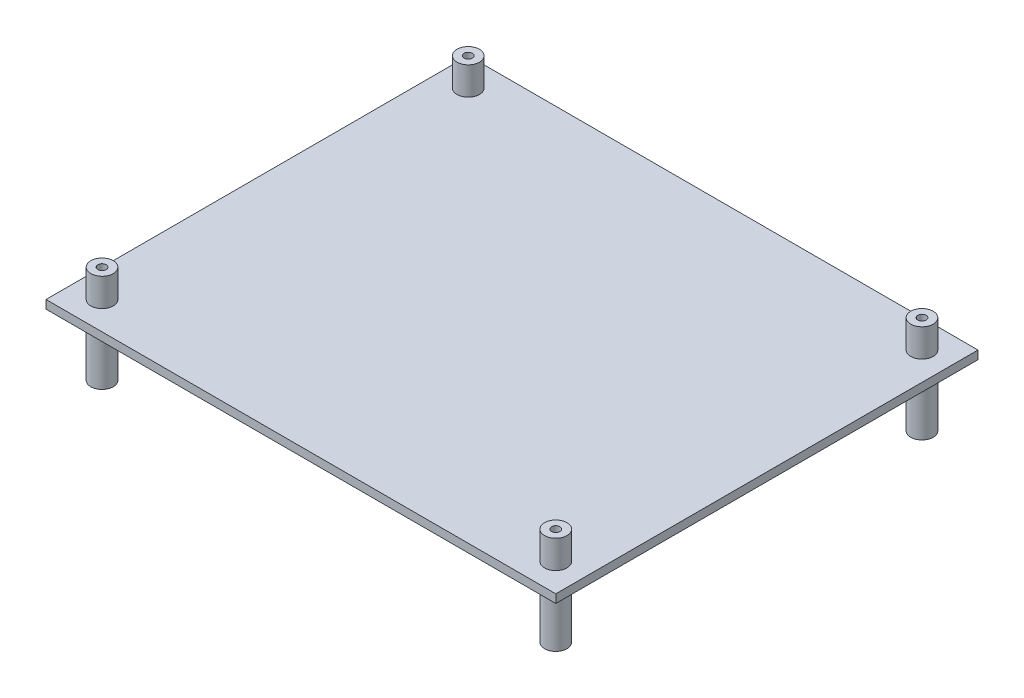
SolidWorks part; units mm, degrees
ref_plane "Front Plane" through (0, 0, 0) normal (0, 0, 1) x (1, 0, 0)
ref_plane "Top Plane" through (0, 0, 0) normal (0, 1, 0) x (1, 0, 0)
ref_plane "Right Plane" through (0, 0, 0) normal (1, 0, 0) x (0, 0, -1)
sketch "Sketch1" plane through (0, 0, 0) normal (0, 1, 0) x (1, 0, 0)
  line L0 (-10, -10) -> (-10, 140.7502)
  line L1 (0, 0) -> (162, 0) construction
  line L2 (0, 0) -> (0, 130.7502) construction
  line L3 (0, 130.7502) -> (162, 130.7502) construction
  line L4 (162, 0) -> (162, 130.7502) construction
  line L5 (-10, 140.7502) -> (172, 140.7502)
  line L6 (172, -10) -> (172, 140.7502)
  line L7 (-10, -10) -> (172, -10)
  circle A0 centre (0, 130.7502) radius 1.5
  circle A1 centre (162, 130.7502) radius 1.5
  circle A2 centre (162, 0) radius 1.5
  circle A3 centre (0, 0) radius 1.5
  dimension "D3" = 3
  dimension "D1" = 130.7502
  dimension "D2" = 162
  dimension "D4" = 10
extrude "Boss-Extrude1" add sketch "Sketch1" along normal blind 3
sketch "Sketch2" plane through (0, 3, 0) normal (0, 1, 0) x (1, 0, 0)
  circle A0 centre (0, 130.7502) radius 4
  circle A1 centre (162, 130.7502) radius 4
  circle A2 centre (162, 0) radius 4
  circle A3 centre (0, 0) radius 4
  circle A4 centre (0, 130.7502) radius 1.5 construction
  circle A5 centre (162, 130.7502) radius 1.5 construction
  circle A6 centre (162, 0) radius 1.5 construction
  circle A7 centre (0, 0) radius 1.5 construction
  circle A8 centre (0, 130.7502) radius 1.5
  circle A9 centre (162, 130.7502) radius 1.5
  circle A10 centre (162, 0) radius 1.5
  circle A11 centre (0, 0) radius 1.5
  dimension "D1" = 8
extrude "Boss-Extrude2" add sketch "Sketch2" along normal blind 10 and the other way blind 25
